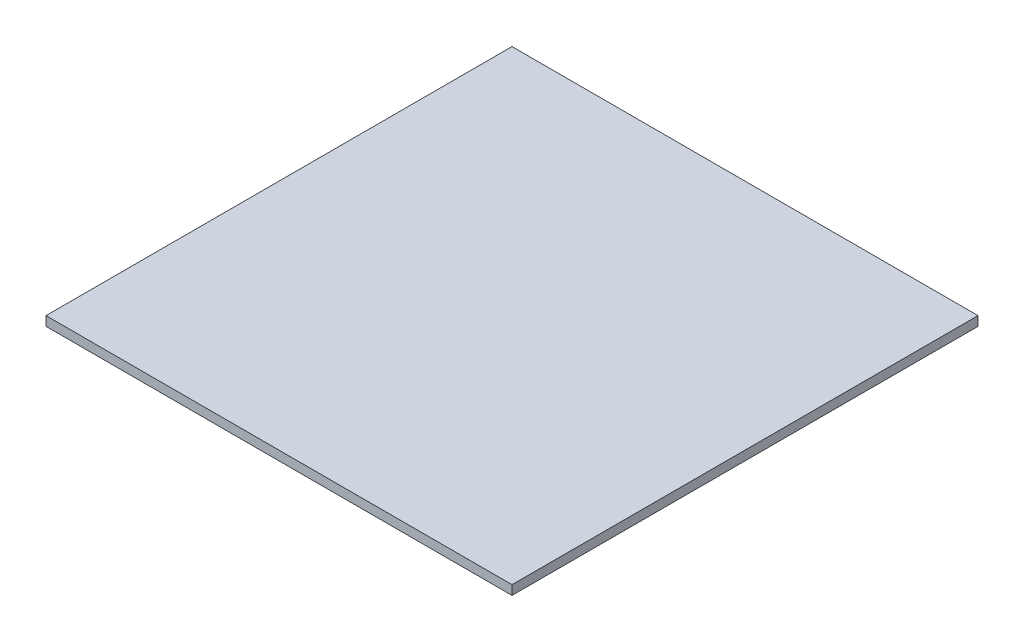
SolidWorks part; units mm, degrees
ref_plane "Front Plane" through (0, 0, 0) normal (0, 0, 1) x (1, 0, 0)
ref_plane "Top Plane" through (0, 0, 0) normal (0, 1, 0) x (1, 0, 0)
ref_plane "Right Plane" through (0, 0, 0) normal (1, 0, 0) x (0, 0, -1)
sketch "Sketch1" plane through (0, 0, 0) normal (0, 1, 0) x (1, 0, 0)
  line L0 (17.3538, 87.1) -> (60.1595, 87.1) construction
  line L1 (11.3706, -19.2693) -> (161.3706, -19.2693)
  line L2 (11.3706, -19.2693) -> (11.3706, 130.7307)
  line L3 (11.3706, 130.7307) -> (161.3706, 130.7307)
  line L4 (161.3706, -19.2693) -> (161.3706, 130.7307)
  line L5 (60.1595, 93.39) -> (60.1595, 86.34) construction
  line L6 (117.3538, 87.1) -> (17.3538, 87.1) construction
  line L7 (60.1595, 87.1) -> (60.1595, 93.39) construction
  line L8 (60.1595, 93.39) -> (78.1595, 93.39) construction
  line L9 (78.1595, 93.39) -> (78.1595, 87.1) construction
  line L10 (78.1595, 93.39) -> (78.1595, 86.34) construction
  line L11 (78.1595, 87.1) -> (117.3538, 87.1) construction
  line L12 (117.3538, 87.1) -> (117.3538, 37.1) construction
  line L13 (117.3538, -12.9) -> (117.3538, 87.1) construction
  line L14 (117.3538, 37.1) -> (138.9303, 36.945) construction
  line L15 (138.9303, 36.945) -> (138.9303, 4.245) construction
  line L16 (138.9303, 4.245) -> (117.3538, 4.245) construction
  line L17 (88.3803, 4.245) -> (138.9303, 4.245) construction
  line L18 (117.3538, 4.245) -> (117.3538, -12.9) construction
  line L19 (117.3538, -12.9) -> (98.2564, -12.9) construction
  line L20 (98.2564, -13.8709) -> (98.2564, 1.3791) construction
  line L21 (17.3538, -12.9) -> (117.3538, -12.9) construction
  line L22 (98.2564, -12.9) -> (98.2564, -13.8709) construction
  line L23 (98.2564, -13.8709) -> (89.2064, -13.8709) construction
  line L24 (89.2064, -13.8709) -> (89.2064, -12.9) construction
  line L25 (89.2064, 1.3791) -> (89.2064, -13.8709) construction
  line L26 (89.2064, -12.9) -> (17.3538, -12.9) construction
  line L27 (17.3538, -12.9) -> (17.3538, 87.1) construction
  circle A0 centre (23.3538, 82.1) radius 1.55 construction
  circle A1 centre (111.3538, 81.1) radius 1.55 construction
  circle A2 centre (23.3538, -7.9) radius 1.55 construction
  circle A3 centre (111.3538, -6.9) radius 1.55 construction
  dimension "D1" = 150
  dimension "D2" = 150
extrude "Boss-Extrude1" add sketch "Sketch1" along normal blind 3
